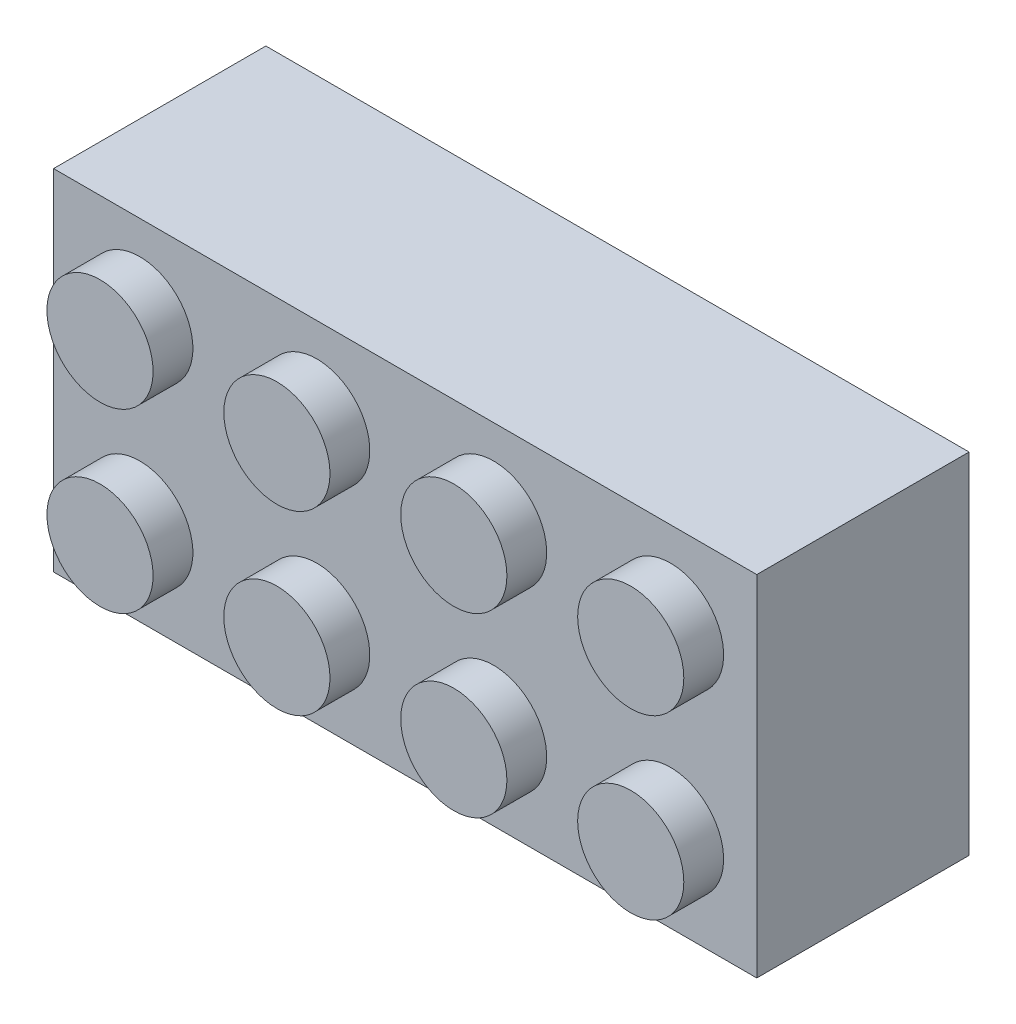
SolidWorks part; units mm, degrees
ref_plane "Front Plane" through (0, 0, 0) normal (0, 0, 1) x (1, 0, 0)
ref_plane "Top Plane" through (0, 0, 0) normal (0, 1, 0) x (1, 0, 0)
ref_plane "Right Plane" through (0, 0, 0) normal (1, 0, 0) x (0, 0, -1)
sketch "Sketch1" plane through (0, 0, 0) normal (0, 0, 1) x (1, 0, 0)
  line L1 (-15.9, -7.9) -> (15.9, -7.9)
  line L2 (-15.9, -7.9) -> (-15.9, 7.9)
  line L3 (-15.9, 7.9) -> (15.9, 7.9)
  line L4 (15.9, -7.9) -> (15.9, 7.9)
  line L5 (-15.9, -7.9) -> (15.9, 7.9) construction
  line L6 (-15.9, 7.9) -> (15.9, -7.9) construction
  point P0 (0, 0)
  dimension "D1" = 15.8
  dimension "D2" = 31.8
extrude "Boss-Extrude1" add sketch "Sketch1" along normal blind 9.6
sketch "Sketch2" plane through (0, 0, 9.6) normal (0, 0, 1) x (1, 0, 0)
  line L0 (-15.9, 0) -> (0, 0) construction
  line L1 (-15.9, 7.9) -> (-15.9, -7.9) construction
  line L2 (0, 0) -> (0, 7.9) construction
  line L3 (15.9, 7.9) -> (-15.9, 7.9) construction
  circle A0 centre (-12, 4) radius 2.4
  circle A1 centre (-4, 4) radius 2.4
  circle A2 centre (4, 4) radius 2.4
  circle A3 centre (12, 4) radius 2.4
  circle A4 centre (-4, -4) radius 2.4
  circle A5 centre (4, -4) radius 2.4
  circle A6 centre (12, -4) radius 2.4
  circle A7 centre (-12, -4) radius 2.4
  dimension "D1" = 4.8
  dimension "D2" = 12
  dimension "D3" = 4
  dimension "D4" = 4
  dimension "D5" = 2
extrude "Boss-Extrude2" add sketch "Sketch2" along normal blind 1.8
sketch "Sketch6" plane through (0, 0, 0) normal (0, 0, -1) x (-1, 0, 0)
  line L0 (15.9, 7.9) -> (15.9, -7.9) construction
  line L1 (-14.7, -6.7) -> (14.7, -6.7)
  line L2 (-14.7, -6.7) -> (-14.7, 6.7)
  line L3 (-14.7, 6.7) -> (14.7, 6.7)
  line L4 (14.7, -6.7) -> (14.7, 6.7)
  line L5 (-14.7, -6.7) -> (14.7, 6.7) construction
  line L6 (-14.7, 6.7) -> (14.7, -6.7) construction
  line L7 (-15.9, 7.9) -> (15.9, 7.9) construction
  line L8 (-12, 6.5) -> (-12, 5.9027) construction
  line L9 (-12.6, 6.7) -> (-11.4, 6.7)
  line L10 (-12.6, 6.7) -> (-12.6, 6.5)
  line L11 (-12.6, 6.5) -> (-11.4, 6.5)
  line L12 (-11.4, 6.7) -> (-11.4, 6.5)
  line L13 (-4.6, 6.7) -> (-4.6, 6.5)
  line L14 (-4.6, 6.7) -> (-3.4, 6.7)
  line L15 (-3.4, 6.7) -> (-3.4, 6.5)
  line L16 (-4.6, 6.5) -> (-3.4, 6.5)
  line L17 (3.4, 6.7) -> (3.4, 6.5)
  line L18 (3.4, 6.7) -> (4.6, 6.7)
  line L19 (4.6, 6.7) -> (4.6, 6.5)
  line L20 (3.4, 6.5) -> (4.6, 6.5)
  line L21 (11.4, 6.7) -> (11.4, 6.5)
  line L22 (11.4, 6.7) -> (12.6, 6.7)
  line L23 (12.6, 6.7) -> (12.6, 6.5)
  line L24 (11.4, 6.5) -> (12.6, 6.5)
  line L25 (-4.6, -6.5) -> (-4.6, -6.7)
  line L26 (-4.6, -6.5) -> (-3.4, -6.5)
  line L27 (-3.4, -6.5) -> (-3.4, -6.7)
  line L28 (-4.6, -6.7) -> (-3.4, -6.7)
  line L29 (3.4, -6.5) -> (3.4, -6.7)
  line L30 (3.4, -6.5) -> (4.6, -6.5)
  line L31 (4.6, -6.5) -> (4.6, -6.7)
  line L32 (3.4, -6.7) -> (4.6, -6.7)
  line L33 (11.4, -6.5) -> (11.4, -6.7)
  line L34 (11.4, -6.5) -> (12.6, -6.5)
  line L35 (12.6, -6.5) -> (12.6, -6.7)
  line L36 (11.4, -6.7) -> (12.6, -6.7)
  line L37 (-12.6, -6.5) -> (-12.6, -6.7)
  line L38 (-12.6, -6.5) -> (-11.4, -6.5)
  line L39 (-11.4, -6.5) -> (-11.4, -6.7)
  line L40 (-12.6, -6.7) -> (-11.4, -6.7)
  line L41 (-14.5, 4) -> (-13.5543, 4) construction
  line L42 (-14.7, 4.6) -> (-14.5, 4.6)
  line L43 (-14.7, 4.6) -> (-14.7, 3.4)
  line L44 (-14.7, 3.4) -> (-14.5, 3.4)
  line L45 (-14.5, 4.6) -> (-14.5, 3.4)
  line L46 (14.5, 4.6) -> (14.5, 3.4)
  line L47 (14.5, 4.6) -> (14.7, 4.6)
  line L48 (14.7, 4.6) -> (14.7, 3.4)
  line L49 (14.5, 3.4) -> (14.7, 3.4)
  line L50 (14.5, -3.4) -> (14.5, -4.6)
  line L51 (14.5, -3.4) -> (14.7, -3.4)
  line L52 (14.7, -3.4) -> (14.7, -4.6)
  line L53 (14.5, -4.6) -> (14.7, -4.6)
  line L54 (-14.7, -3.4) -> (-14.7, -4.6)
  line L55 (-14.7, -3.4) -> (-14.5, -3.4)
  line L56 (-14.5, -3.4) -> (-14.5, -4.6)
  line L57 (-14.7, -4.6) -> (-14.5, -4.6)
  point P0 (0, 0)
  dimension "D1" = 1.2
  dimension "D2" = 1.2
  dimension "D3" = 0.2
  dimension "D4" = 1.2
  dimension "D5" = 12
  dimension "D8" = 1.2
  dimension "D9" = 0.2
  dimension "D10" = 4
  dimension "D6" = 4
  dimension "D7" = 2
  dimension "D11" = 2
  dimension "D12" = 2
extrude "Cut-Extrude3" cut sketch "Sketch6" against normal offset from surface (8.6 mm away) 1 contours L57 L2 L1 L37 L38 L39 L25 L26 L27 L29 L30 L31 L33 L34 L35 L4 L53 L50 L51 L49 L46 L47 L3 L23 L24 L21 L19 L20 L17 L15 L16 L13 L12 L11 L10 L42 L45 L44 L55
sketch "Sketch7" plane through (0, 0, 8.6) normal (0, 0, -1) x (-1, 0, 0)
  circle A2 centre (-12, 4) radius 1.3
  circle A3 centre (-4, 4) radius 1.3
  circle A4 centre (4, 4) radius 1.3
  circle A5 centre (12, 4) radius 1.3
  circle A6 centre (-4, -4) radius 1.3
  circle A7 centre (4, -4) radius 1.3
  circle A8 centre (12, -4) radius 1.3
  circle A9 centre (-12, -4) radius 1.3
  dimension "D1" = 2.6
  dimension "D2" = 4
  dimension "D3" = 2
extrude "Cut-Extrude4" cut sketch "Sketch7" against normal offset from surface (1.7 mm away) 1.1 up to face at (14.4, 4, 11.4)
sketch "Sketch8" plane through (0, 0, 8.6) normal (0, 0, -1) x (-1, 0, 0)
  circle A0 centre (0, 0) radius 3.25
  circle A1 centre (0, 0) radius 2.05
  circle A2 centre (8, 0) radius 2.05
  circle A3 centre (8, 0) radius 3.25
  circle A4 centre (0, 0) radius 2.05
  circle A5 centre (0, 0) radius 3.25
  circle A6 centre (-8, 0) radius 2.05
  circle A7 centre (-8, 0) radius 3.25
  dimension "D1" = 6.5
  dimension "D2" = 1.2
  dimension "D3" = 2
  dimension "D4" = 2
extrude "Boss-Extrude4" add sketch "Sketch8" along normal up to surface (8.6 mm away) contours A7 A6 | A0 A1 | A3 A2 up to face at (0, 0, 0)
sketch "Sketch9" plane through (0, 0, 8.6) normal (0, 0, -1) x (-1, 0, 0)
  line L0 (3.4, 6.7) -> (-3.4, 6.7) construction
  line L1 (-0.55, -6.7) -> (0.55, -6.7)
  line L2 (-0.55, -6.7) -> (-0.55, -3.2031)
  line L3 (-0.55, 6.7) -> (0.55, 6.7)
  line L4 (0.55, -6.7) -> (0.55, -3.2031)
  line L5 (-0.55, -6.7) -> (-0.2659, -3.2391) construction
  line L6 (-0.55, 6.7) -> (-0.2659, 3.2391) construction
  line L7 (-0.55, 3.2031) -> (-0.55, 6.7)
  line L8 (0.2659, -3.2391) -> (0.55, -6.7) construction
  line L9 (0.2659, 3.2391) -> (0.55, 6.7) construction
  line L10 (0.55, 3.2031) -> (0.55, 6.7)
  arc A0 (0.55, 3.2031) -> (-0.55, 3.2031) centre (0, 0) ccw
  circle A1 centre (0, 0) radius 3.25
  arc A2 (-0.55, -3.2031) -> (0.55, -3.2031) centre (0, 0) ccw
  dimension "D2" = 1.1
  dimension "D1" = 0
extrude "Boss-Extrude5" add sketch "Sketch9" along normal offset from surface (6.3 mm away) 2.3 contours A0 L10 L3 L7 | A2 L2 L1 L4 up to face at (5.95, 0, 0)
